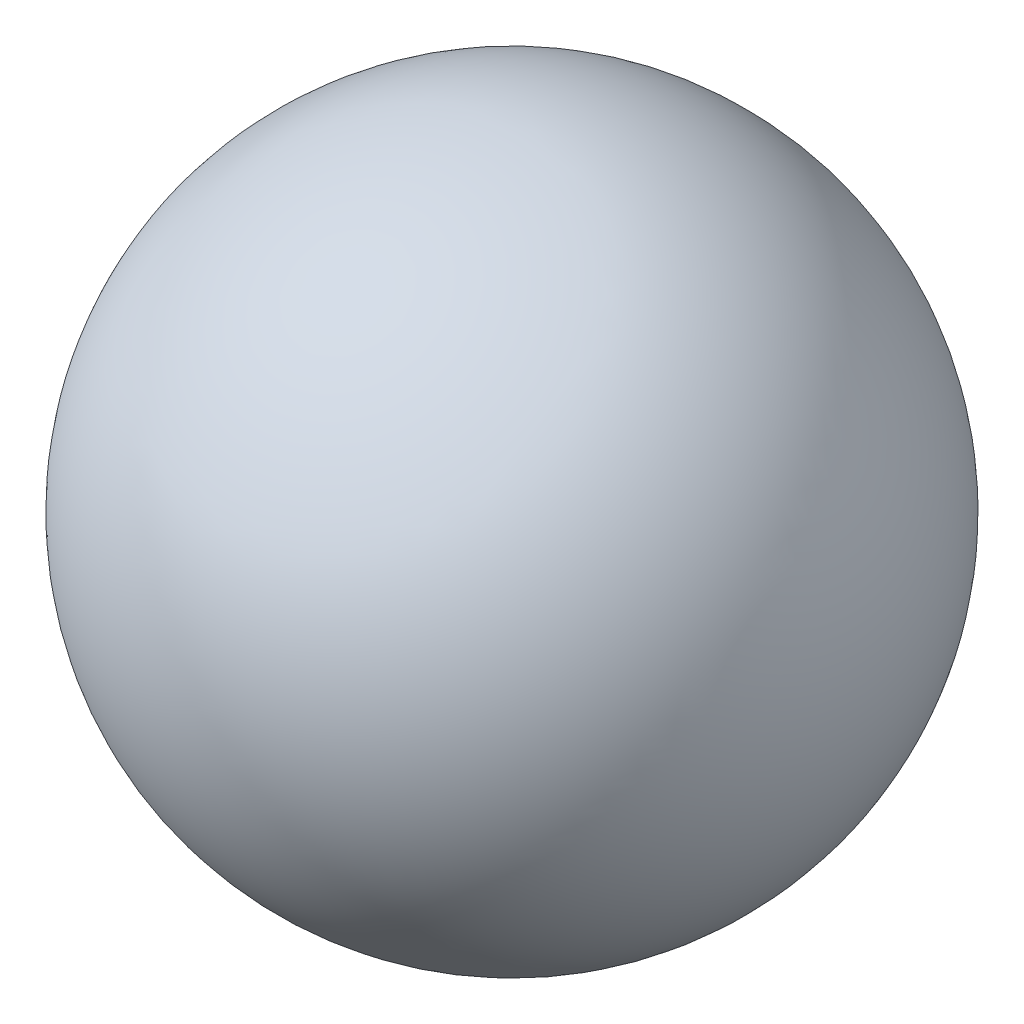
SolidWorks part; units mm, degrees
ref_plane "Front Plane" through (0, 0, 0) normal (0, 0, 1) x (1, 0, 0)
ref_plane "Top Plane" through (0, 0, 0) normal (0, 1, 0) x (1, 0, 0)
ref_plane "Right Plane" through (0, 0, 0) normal (1, 0, 0) x (0, 0, -1)
sketch "Sketch1" plane through (0, 0, 0) normal (0, 0, 1) x (1, 0, 0)
  line L2 (-15.2756, 0) -> (17.7925, 0) construction
  line L3 (-4.2333, 0) -> (4.2333, 0)
  arc A1 (4.2333, 0) -> (-4.2333, 0) centre (0, 0) ccw
  dimension "D1" = 4.2333
revolve "Revolve1" add sketch "Sketch1" angle 360 about L2
